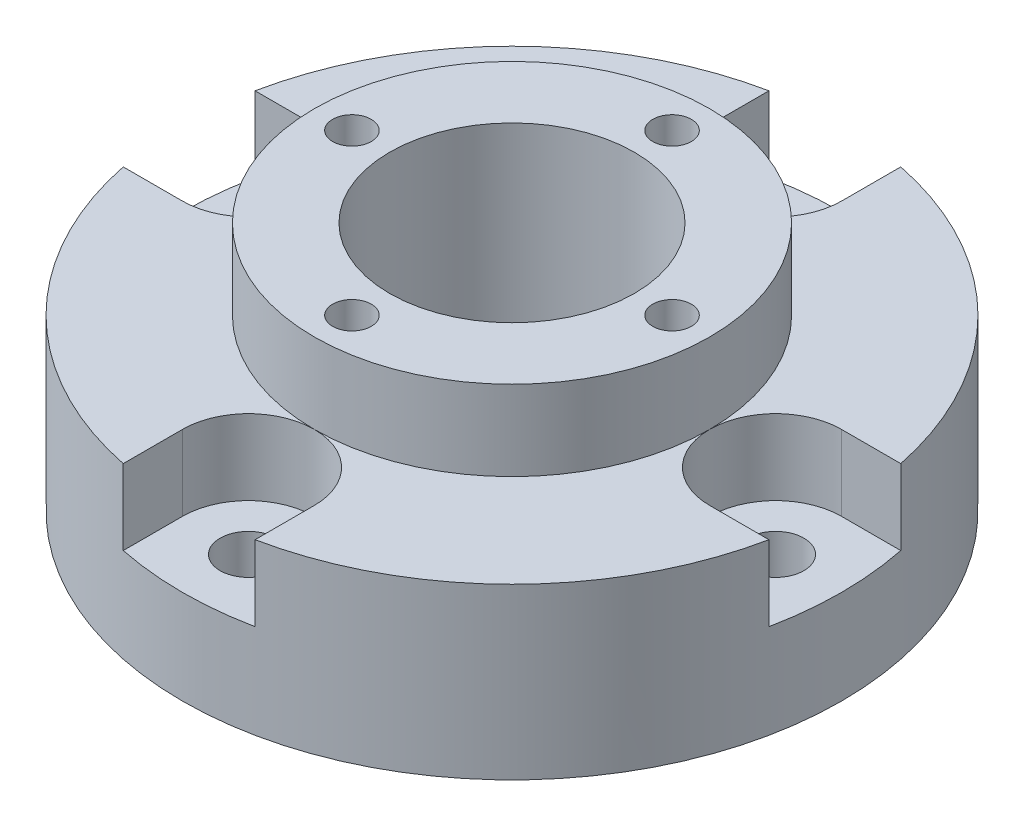
SolidWorks part; units mm, degrees
ref_plane "Спереди" through (0, 0, 0) normal (0, 0, 1) x (1, 0, 0)
ref_plane "Сверху" through (0, 0, 0) normal (0, 1, 0) x (1, 0, 0)
ref_plane "Справа" through (0, 0, 0) normal (1, 0, 0) x (0, 0, -1)
sketch "Эскиз1" plane through (0, 0, 0) normal (0, 0, 1) x (1, 0, 0)
  line L0 (0, 0) -> (0, 37.2504) construction
  line L1 (-13, 0) -> (-13, 26.5)
  line L2 (-13, 26.5) -> (-21, 26.5)
  line L3 (-21, 26.5) -> (-21, 18)
  line L4 (-21, 18) -> (-35, 18)
  line L5 (-35, 18) -> (-35, 0)
  line L6 (-35, 0) -> (-13, 0)
  point P5 (0, 0)
  dimension "D1" = 26.5
  dimension "D2" = 26
  dimension "D3" = 42
  dimension "D4" = 70
  dimension "D5" = 18
revolve "Повернуть1" add sketch "Эскиз1" angle 360 about L0
hole_wizard "Диаметр отверстия Ø4.1 (4.1)1" positions "Эскиз5" profile "Эскиз6" hole size "Ø4.1" standard "DIN" end condition up to next
sketch "Эскиз5" plane through (0, 26.5, 0) normal (0, 1, 0) x (1, 0, 0)
  point P0 (17, 0)
  point P3 (0, 0)
  dimension "D1" = 17
sketch "Эскиз6" plane through (17, 26.5, 0) normal (1, 0, 0) x (0, 0, 1)
  line L0 (0, 0) -> (0, 26.501)
  line L1 (0, 26.501) -> (2.05, 26.501)
  line L2 (2.05, 26.501) -> (2.05, 0)
  line L5 (2.05, 0) -> (0, 0)
  line L11 (0, -6.35) -> (0, 107.95) construction
  dimension "Диаметр сквозного отверстия" = 4.1
  dimension "Глубина сквозного отверстия" = 26.501
hole_wizard "Диаметр отверстия Ø6.0 (6)1" positions "Эскиз2" profile "Эскиз3" hole size "Ø6.0" standard "DIN" end condition up to next
sketch "Эскиз2" plane through (0, 18, 0) normal (0, 1, 0) x (1, 0, 0)
  point P0 (28, 0)
  dimension "D1" = 28
sketch "Эскиз3" plane through (28, 18, 0) normal (1, 0, 0) x (0, 0, 1)
  line L0 (0, 0) -> (0, 18.001)
  line L1 (0, 18.001) -> (3, 18.001)
  line L2 (3, 18.001) -> (3, 0)
  line L5 (3, 0) -> (0, 0)
  line L11 (0, -6.35) -> (0, 107.95) construction
  dimension "Диаметр сквозного отверстия" = 6
  dimension "Глубина сквозного отверстия" = 18.001
sketch "Эскиз4" plane through (0, 18, 0) normal (0, 1, 0) x (1, 0, 0)
  line L0 (28, 7) -> (48, 7)
  line L1 (28, -7) -> (48, -7)
  line L2 (48, -7) -> (48, 7)
  arc A0 (28, 7) -> (28, -7) centre (28, 0) ccw
  dimension "D1" = 14
  dimension "D2" = 20
extrude "Вырез-Вытянуть1" cut sketch "Эскиз4" against normal blind 8
pattern_circular "Круговой массив1" count 4 over 360 about axis through (0, 0, 0) along (0, 1, 0) of "Диаметр отверстия Ø6.0 (6)1", "Вырез-Вытянуть1", "Диаметр отверстия Ø4.1 (4.1)1"
